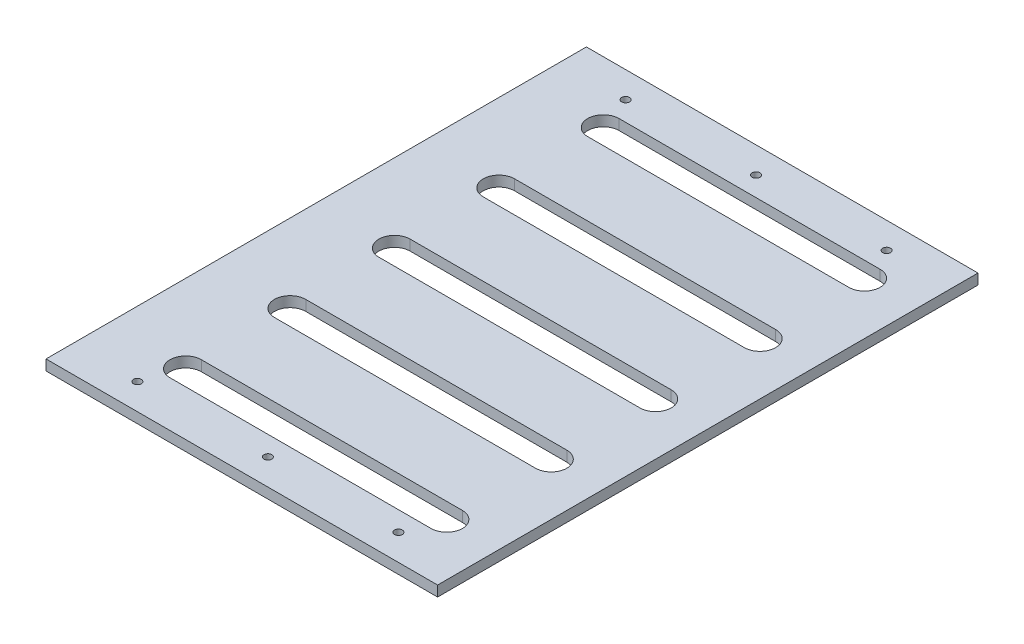
SolidWorks part; units mm, degrees
ref_plane "Front" through (0, 0, 0) normal (0, 0, 1) x (1, 0, 0)
ref_plane "Top" through (0, 0, 0) normal (0, 1, 0) x (1, 0, 0)
ref_plane "Right" through (0, 0, 0) normal (1, 0, 0) x (0, 0, -1)
sketch "草图1" plane through (0, 0, 0) normal (0, 1, 0) x (1, 0, 0)
  line L1 (0, 0) -> (150, 0)
  line L2 (0, 0) -> (0, 207)
  line L3 (0, 207) -> (150, 207)
  line L4 (150, 0) -> (150, 207)
  dimension "D1" = 150
  dimension "D2" = 207
extrude "凸台-拉伸1" add sketch "草图1" along normal blind 4
sketch "草图2" plane through (0, 4, 0) normal (0, 1, 0) x (1, 0, 0)
  line L0 (30, 183.5) -> (130, 183.5) construction
  line L1 (30, 189.5) -> (130, 189.5)
  line L2 (30, 177.5) -> (130, 177.5)
  line L4 (150, 103.5) -> (0, 103.5) construction
  line L5 (150, 0) -> (150, 207) construction
  line L6 (0, 207) -> (0, 0) construction
  line L7 (30, 143.5) -> (130, 143.5) construction
  line L8 (30, 149.5) -> (130, 149.5)
  line L9 (30, 137.5) -> (130, 137.5)
  line L13 (30, 103.5) -> (130, 103.5) construction
  line L14 (30, 97.5) -> (130, 97.5)
  line L15 (30, 109.5) -> (130, 109.5)
  line L16 (30, 63.5) -> (130, 63.5) construction
  line L17 (30, 57.5) -> (130, 57.5)
  line L18 (30, 69.5) -> (130, 69.5)
  line L19 (30, 23.5) -> (130, 23.5) construction
  line L20 (30, 17.5) -> (130, 17.5)
  line L21 (30, 29.5) -> (130, 29.5)
  line L24 (30, 103.5) -> (130, 103.5) construction
  line L25 (30, 109.5) -> (130, 109.5)
  line L26 (30, 97.5) -> (130, 97.5)
  line L27 (30, 103.5) -> (130, 103.5) construction
  line L28 (30, 109.5) -> (130, 109.5)
  line L29 (30, 97.5) -> (130, 97.5)
  arc A0 (30, 189.5) -> (30, 177.5) centre (30, 183.5) ccw
  arc A1 (130, 177.5) -> (130, 189.5) centre (130, 183.5) ccw
  arc A2 (30, 149.5) -> (30, 137.5) centre (30, 143.5) ccw
  arc A3 (130, 137.5) -> (130, 149.5) centre (130, 143.5) ccw
  arc A6 (30, 97.5) -> (30, 109.5) centre (30, 103.5) cw
  arc A7 (130, 109.5) -> (130, 97.5) centre (130, 103.5) cw
  arc A8 (30, 57.5) -> (30, 69.5) centre (30, 63.5) cw
  arc A9 (130, 69.5) -> (130, 57.5) centre (130, 63.5) cw
  arc A10 (30, 17.5) -> (30, 29.5) centre (30, 23.5) cw
  arc A11 (130, 29.5) -> (130, 17.5) centre (130, 23.5) cw
  arc A16 (30, 109.5) -> (30, 97.5) centre (30, 103.5) ccw
  arc A17 (130, 97.5) -> (130, 109.5) centre (130, 103.5) ccw
  point P2 (80, 183.5)
  point P16 (80, 143.5)
  point P29 (80, 103.5)
  point P36 (80, 63.5)
  point P43 (80, 23.5)
  point P50 (80, 103.5)
  point P57 (80, 103.5)
  point P64 (80, 103.5)
  dimension "D2" = 6
  dimension "D1" = 80
  dimension "D3" = 30
  dimension "D4" = 100
  dimension "D5" = 3
extrude "切除-拉伸1" cut sketch "草图2" against normal through all
sketch "草图3" plane through (0, 4, 0) normal (0, 1, 0) x (1, 0, 0)
  line L0 (0, 197) -> (150, 197) construction
  line L1 (0, 207) -> (0, 0) construction
  line L2 (150, 0) -> (150, 207) construction
  line L3 (150, 10) -> (0, 10) construction
  line L4 (150, 207) -> (0, 207) construction
  line L6 (0, 0) -> (150, 0) construction
  line L7 (0, 103.5) -> (150, 103.5) construction
  circle A0 centre (125, 197) radius 1.5
  circle A1 centre (75, 197) radius 1.5
  circle A2 centre (25, 197) radius 1.5
  circle A3 centre (25, 10) radius 1.5
  circle A4 centre (75, 10) radius 1.5
  circle A5 centre (125, 10) radius 1.5
  dimension "D3" = 3
  dimension "D4" = 3
  dimension "D5" = 3
  dimension "D1" = 10
  dimension "D2" = 10
  dimension "D6" = 25
  dimension "D7" = 25
extrude "切除-拉伸2" cut sketch "草图3" against normal through all
